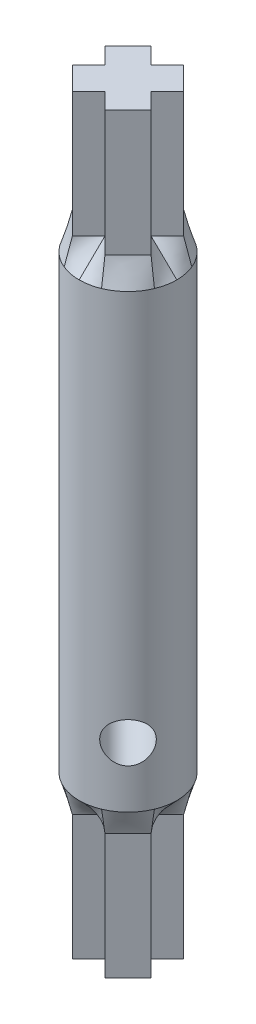
SolidWorks part; units mm, degrees
ref_plane "Front Plane" through (0, 0, 0) normal (0, 0, 1) x (1, 0, 0)
ref_plane "Top Plane" through (0, 0, 0) normal (0, 1, 0) x (1, 0, 0)
ref_plane "Right Plane" through (0, 0, 0) normal (1, 0, 0) x (0, 0, -1)
sketch "Sketch1" plane through (0, 0, 0) normal (0, 1, 0) x (1, 0, 0)
  line L0 (-0.627, 2.9162) -> (-2.423, 4.7122)
  line L1 (-3.167, -2.1638) -> (1.913, -2.1638) construction
  line L2 (-3.167, -2.1638) -> (-3.167, 2.9162) construction
  line L3 (-3.167, 2.9162) -> (1.913, 2.9162) construction
  line L4 (1.913, -2.1638) -> (1.913, 2.9162) construction
  line L5 (-3.167, -2.1638) -> (1.913, 2.9162) construction
  line L6 (-3.167, 2.9162) -> (1.913, -2.1638) construction
  line L7 (-3.167, 0.3762) -> (-4.963, 2.1722)
  line L8 (-4.963, 2.1722) -> (-2.423, 4.7122)
  line L9 (1.913, 0.3762) -> (3.7091, -1.4199)
  line L10 (-0.627, -2.1638) -> (1.1691, -3.9599)
  line L11 (1.1691, -3.9599) -> (3.7091, -1.4199)
  line L12 (-3.167, 0.3762) -> (-4.963, -1.4199)
  line L13 (-0.627, -2.1638) -> (-2.423, -3.9599)
  line L14 (-4.963, -1.4199) -> (-2.423, -3.9599)
  line L15 (1.913, 0.3762) -> (3.7091, 2.1722)
  line L16 (1.1691, 4.7122) -> (3.7091, 2.1722)
  line L17 (-0.627, 2.9162) -> (1.1691, 4.7122)
  point P0 (-0.627, 0.3762)
  dimension "D1" = 2.54
  dimension "D2" = 5.08
  dimension "D3" = 5.08
  dimension "D4" = 8.6721
  dimension "D5" = 3.5921
  dimension "D6" = 3.5921
  dimension "D7" = 3.5921
  dimension "D8" = 3.5921
  dimension "D9" = 8.6721
  dimension "D10" = 0
  dimension "D11" = 3.5921
  dimension "D12" = 5.08
  dimension "D13" = 2.54
  dimension "D14" = 2.54
  dimension "D15" = 2.54
  dimension "D16" = 2.54
  dimension "D17" = 2.54
  dimension "D18" = 2.54
  dimension "D19" = 2.54
  dimension "D20" = 2.54
extrude "Boss-Extrude1" add sketch "Sketch1" along normal blind 13.8043
scale "Scale1" scale about centroid uniform scaling yes scale factor 0.92
ref_plane "Plane1" through (0, 15.7922, 0) normal (0, 1, 0) x (1, 0, 0)
sketch "Sketch2" plane through (0, 15.7922, 0) normal (0, 1, 0) x (1, 0, 0)
  line L0 (-2.9638, 0.3762) -> (1.7098, 0.3762) construction
  line L1 (-0.627, 2.713) -> (-0.627, -1.9606) construction
  circle A0 centre (-0.627, 0.3762) radius 4.953
  dimension "D1" = 9.906
loft "Loft1" add profiles "Sketch2" section face at (-0.627, 13.2522, -0.3762) section "Sketch2"
sketch "Sketch3" plane through (0, 15.7922, 0) normal (0, 1, 0) x (1, 0, 0)
  circle A0 centre (-0.627, 0.3762) radius 4.953
extrude "Boss-Extrude2" add sketch "Sketch3" along normal blind 22.86
mirror "Mirror6" about plane through (-0.627, 38.6522, -0.3762) normal (0, 1, 0) of "Boss-Extrude2"
ref_plane "Plane3" through (0, 63.501, 0) normal (0, 1, 0) x (1, 0, 0)
sketch "Sketch5" plane through (0, 63.501, 0) normal (0, 1, 0) x (1, 0, 0)
  line L0 (-0.627, 2.9162) -> (-2.423, 4.7122)
  line L1 (-3.167, -2.1638) -> (1.913, -2.1638) construction
  line L2 (-3.167, -2.1638) -> (-3.167, 2.9162) construction
  line L3 (-3.167, 2.9162) -> (1.913, 2.9162) construction
  line L4 (1.913, -2.1638) -> (1.913, 2.9162) construction
  line L5 (-3.167, -2.1638) -> (1.913, 2.9162) construction
  line L6 (-3.167, 2.9162) -> (1.913, -2.1638) construction
  line L7 (-3.167, 0.3762) -> (-4.963, 2.1722)
  line L8 (-4.963, 2.1722) -> (-2.423, 4.7122)
  line L9 (1.913, 0.3762) -> (3.7091, -1.4199)
  line L10 (-0.627, -2.1638) -> (1.1691, -3.9599)
  line L11 (1.1691, -3.9599) -> (3.7091, -1.4199)
  line L12 (-3.167, 0.3762) -> (-4.963, -1.4199)
  line L13 (-0.627, -2.1638) -> (-2.423, -3.9599)
  line L14 (-4.963, -1.4199) -> (-2.423, -3.9599)
  line L15 (1.913, 0.3762) -> (3.7091, 2.1722)
  line L16 (1.1691, 4.7122) -> (3.7091, 2.1722)
  line L17 (-0.627, 2.9162) -> (1.1691, 4.7122)
  line L18 (-0.627, 5.3292) -> (-0.627, 0.3762) construction
  line L19 (-0.627, 0.3762) -> (-5.58, 0.3762) construction
  circle A0 centre (-0.627, 0.3762) radius 4.953 construction
  point P0 (-0.627, 0.3762)
  dimension "D1" = 2.54
  dimension "D2" = 5.08
  dimension "D3" = 5.08
  dimension "D4" = 8.6721
  dimension "D5" = 3.5921
  dimension "D6" = 3.5921
  dimension "D7" = 3.5921
  dimension "D8" = 3.5921
  dimension "D9" = 8.6721
  dimension "D10" = 0
  dimension "D11" = 3.5921
  dimension "D12" = 5.08
  dimension "D13" = 2.54
  dimension "D14" = 2.54
  dimension "D15" = 2.54
  dimension "D16" = 2.54
  dimension "D17" = 2.54
  dimension "D18" = 2.54
  dimension "D19" = 2.54
  dimension "D20" = 2.54
extrude "Boss-Extrude4" add sketch "Sketch5" along normal blind 13.8043 separate body
scale "Scale2" bodies to scale 108 scale about centroid uniform scaling yes scale factor 0.92
loft "Loft2" add section face at (-0.627, 61.5122, 4.5768) section face at (-0.627, 64.0532, -0.3762)
ref_plane "Plane4" through (-4.0039, 0, -4.0039) normal (-0.7071, 0, -0.7071) x (-0.7071, 0, 0.7071)
sketch "Sketch6" plane through (-4.0039, 0, -4.0039) normal (-0.7071, 0, -0.7071) x (-0.7071, 0, 0.7071)
  line L0 (5.1303, 59.783) -> (-4.7757, 59.783) construction
  line L1 (5.1303, 15.7922) -> (5.1303, 61.5122) construction
  line L2 (-4.7757, 61.5122) -> (-4.7757, 15.7922) construction
  line L3 (0.1773, 59.783) -> (0.1773, 61.5122) construction
  line L4 (0.1773, 61.5122) -> (0.1773, 15.7922) construction
  line L5 (-1.7181, 15.7922) -> (2.0728, 15.7922) construction
  line L6 (0.1773, 38.6522) -> (9.0518, 38.6522) construction
  circle A0 centre (0.1773, 21.8882) radius 2.032
  spline S0 degree 3 poles (-1.7181, 61.5122) (-1.4165, 61.5122) (-1.1068, 61.5094) (-0.4717, 61.5098) (-0.1447, 61.5122) (0.4999, 61.5122) (0.8204, 61.5098) (1.4581, 61.5094) (1.7712, 61.5122) (2.0728, 61.5122) knots 0 0 0 0 0.25 0.25 0.5 0.5 0.75 0.75 1 1 1 1 construction
  dimension "D1" = 4.064
  dimension "D2" = 6.096
extrude "Cut-Extrude1" cut sketch "Sketch6" against normal through all
